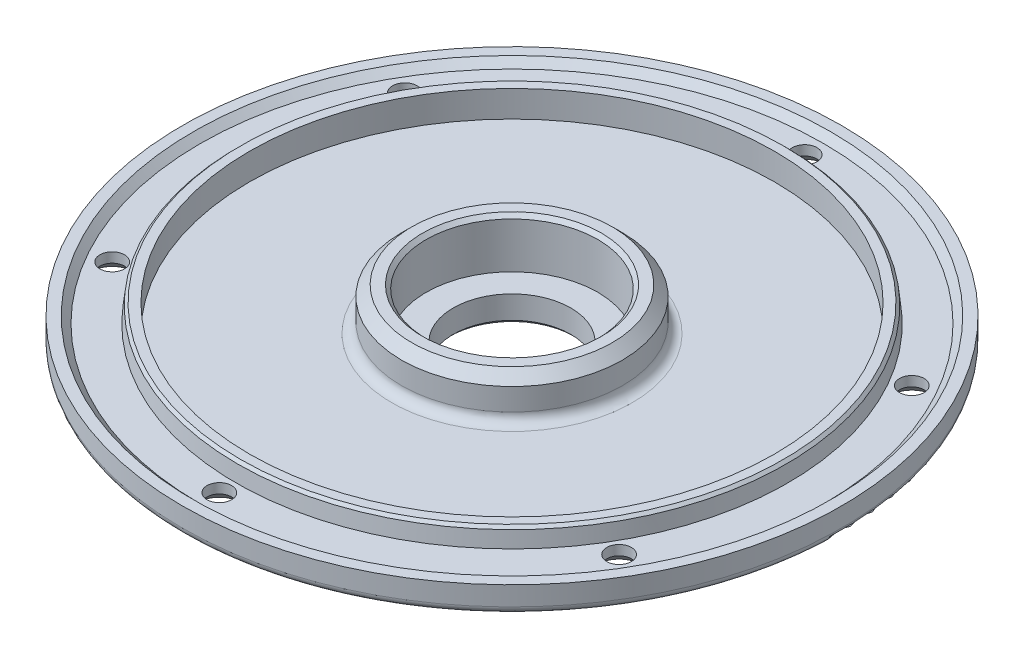
SolidWorks part; units mm, degrees
ref_plane "Plan de face" through (0, 0, 0) normal (0, 0, 1) x (1, 0, 0)
ref_plane "Plan de dessus" through (0, 0, 0) normal (0, 1, 0) x (1, 0, 0)
ref_plane "Plan de droite" through (0, 0, 0) normal (1, 0, 0) x (0, 0, -1)
sketch "Esquisse2" plane through (0, 0, 0) normal (0, 0, 1) x (1, 0, 0)
  line L0 (0, 0) -> (0, 94.8214) construction
  line L1 (-11.95, 56.6) -> (-17.45, 56.6)
  line L2 (-17.45, 56.6) -> (-17.45, 65.9)
  line L3 (-17.45, 65.9) -> (-18.2, 66.65)
  line L4 (-18.2, 66.65) -> (-20.4, 66.65)
  line L5 (-20.4, 66.65) -> (-22.45, 64.6)
  line L6 (-22.45, 64.6) -> (-22.45, 60.1)
  line L7 (-11.95, 56.6) -> (-11.95, 51.95)
  line L8 (-11.95, 51.95) -> (-12.7, 51.2)
  line L9 (-12.7, 51.2) -> (-15, 51.2)
  line L10 (-15, 51.2) -> (-21.9, 55.8)
  line L11 (-21.9, 55.8) -> (-65.5, 55.8)
  line L12 (-67, 57.3) -> (-67, 61.2)
  line L13 (-67, 61.2) -> (-64.8, 61.2)
  line L14 (-64.8, 61.2) -> (-63.4, 59.8)
  line L15 (-63.4, 59.8) -> (-56.1, 59.8)
  line L16 (-22.45, 60.1) -> (-24.45, 60.1) construction
  line L17 (-56.1, 59.8) -> (-55.75, 62.95)
  line L18 (-55.75, 62.95) -> (-55.2, 63.5)
  line L20 (-55.2, 63.5) -> (-53.35, 63.5)
  line L21 (-53.35, 63.5) -> (-53.35, 58.1)
  line L22 (-53.35, 58.1) -> (-24.45, 58.1)
  line L23 (-24.45, 60.1) -> (-24.45, 58.1) construction
  arc A1 (-67, 57.3) -> (-65.5, 55.8) centre (-65.5, 57.3) ccw
  arc A2 (-22.45, 60.1) -> (-24.45, 58.1) centre (-24.45, 60.1) cw
  dimension "D2" = 3
  dimension "D27" = 2
  dimension "D3" = 11.95
  dimension "D4" = 5.5
  dimension "D5" = 9.3
  dimension "D6" = 0.75
  dimension "D7" = 0.75
  dimension "D8" = 2.2
  dimension "D9" = 5.4
  dimension "D10" = 0.75
  dimension "D11" = 0.75
  dimension "D13" = 6.9
  dimension "D14" = 4.6
  dimension "D15" = 2.3
  dimension "D16" = 43.6
  dimension "D17" = 3.9
  dimension "D18" = 2.2
  dimension "D19" = 1.4
  dimension "D20" = 1.4
  dimension "D21" = 7.3
  dimension "D22" = 0.35
  dimension "D23" = 3.15
  dimension "D24" = 0.55
  dimension "D25" = 5.4
  dimension "D28" = 2.75
  dimension "D30" = 5
revolve "Révolution1" add sketch "Esquisse2" angle 360 about L0
sketch "Esquisse3" plane through (0, 55.8, 0) normal (0, -1, 0) x (1, 0, 0)
  line L0 (0, 0) -> (0, 59.5) construction
  circle A0 centre (0, 59.5) radius 2.5
  dimension "D2" = 5
  dimension "D1" = 59.5
extrude "Enlèv. mat.-Extru.1" cut sketch "Esquisse3" against normal through all
chamfer "Chanfrein1" distance 2 distance2 2 1 edges at (0, 55.8, 57)
pattern_circular "Répétition circulaire1" count 6 over 360 about axis through (0, 0, 0) along (0, 1, 0) of "Enlèv. mat.-Extru.1", "Chanfrein1"
